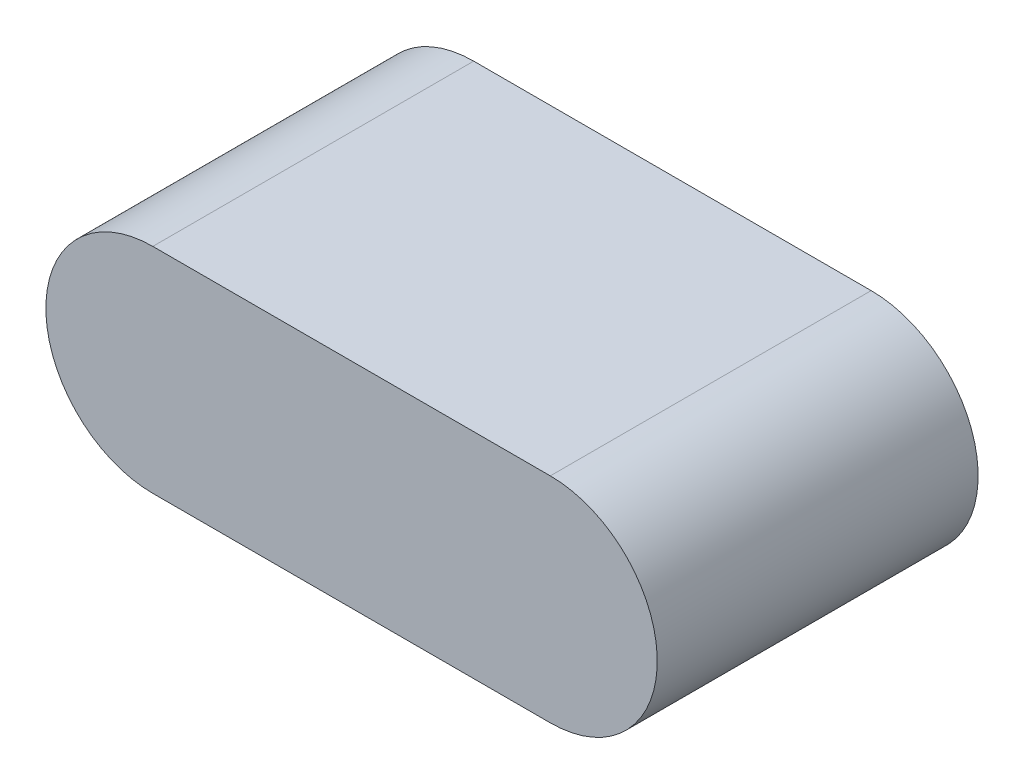
SolidWorks part; units mm, degrees
ref_plane "Front Plane" through (0, 0, 0) normal (0, 0, 1) x (1, 0, 0)
ref_plane "Top Plane" through (0, 0, 0) normal (0, 1, 0) x (1, 0, 0)
ref_plane "Right Plane" through (0, 0, 0) normal (1, 0, 0) x (0, 0, -1)
sketch "Sketch1" plane through (0, 0, 0) normal (0, 0, 1) x (1, 0, 0)
  line L0 (-27.0764, -14.5196) -> (-23.3602, -14.5196) construction
  line L1 (-27.0764, -13.5196) -> (-23.3602, -13.5196)
  line L2 (-27.0764, -15.5196) -> (-23.3602, -15.5196)
  arc A0 (-27.0764, -13.5196) -> (-27.0764, -15.5196) centre (-27.0764, -14.5196) ccw
  arc A1 (-23.3602, -15.5196) -> (-23.3602, -13.5196) centre (-23.3602, -14.5196) ccw
  point P2 (-25.2183, -14.5196)
extrude "Boss-Extrude1" add sketch "Sketch1" along normal blind 3
